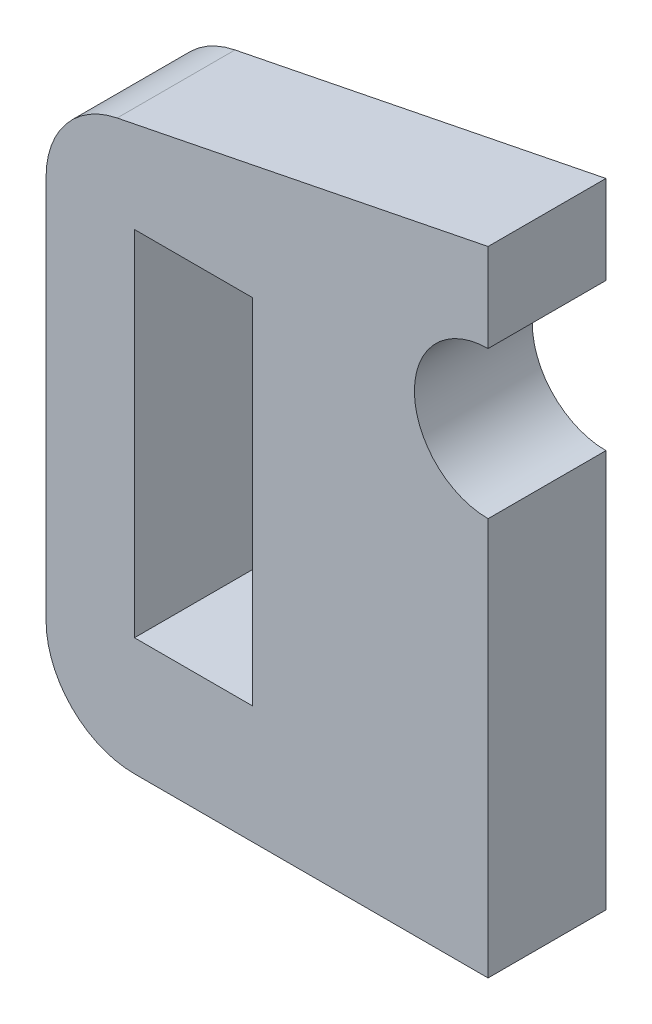
SolidWorks part; units mm, degrees
material "ﾊﾞﾙｻ"
ref_plane "正面" through (0, 0, 0) normal (0, 0, 1) x (1, 0, 0)
ref_plane "平面" through (0, 0, 0) normal (0, 1, 0) x (1, 0, 0)
ref_plane "右側面" through (0, 0, 0) normal (1, 0, 0) x (0, 0, -1)
sketch "ｽｹｯﾁ1" plane through (0, 0, 0) normal (0, 0, 1) x (1, 0, 0)
  line L0 (0, 5.5) -> (-15, 2.5)
  line L1 (-15, 2.5) -> (-15, -16)
  line L2 (-15, -16) -> (0, -16)
  line L3 (0, -16) -> (0, 5.5)
  line L4 (-15, 2.5) -> (0, 2.5) construction
  line L5 (-8, -12) -> (-12, -12)
  line L6 (-8, -12) -> (-8, 0)
  line L7 (-8, 0) -> (-12, 0)
  line L8 (-12, -12) -> (-12, 0)
  line L9 (-8, -12) -> (-12, 0) construction
  line L10 (-8, 0) -> (-12, -12) construction
  circle A0 centre (0, 0) radius 2.5
  point P8 (-10, -6)
  dimension "D1" = 5
  dimension "D2" = 4
  dimension "D3" = 3
  dimension "D4" = 4
  dimension "D5" = 8
  dimension "D6" = 3
  dimension "D7" = 12
extrude "ﾎﾞｽ - 押し出し1" add sketch "ｽｹｯﾁ1" along normal blind 4 contours A0 L3 L0 L1 L2 L5 L8 L7 L6
fillet "ﾌｨﾚｯﾄ1" radius 3 2 edges at (-15, 2.5, 2) (-15, -16, 2)
